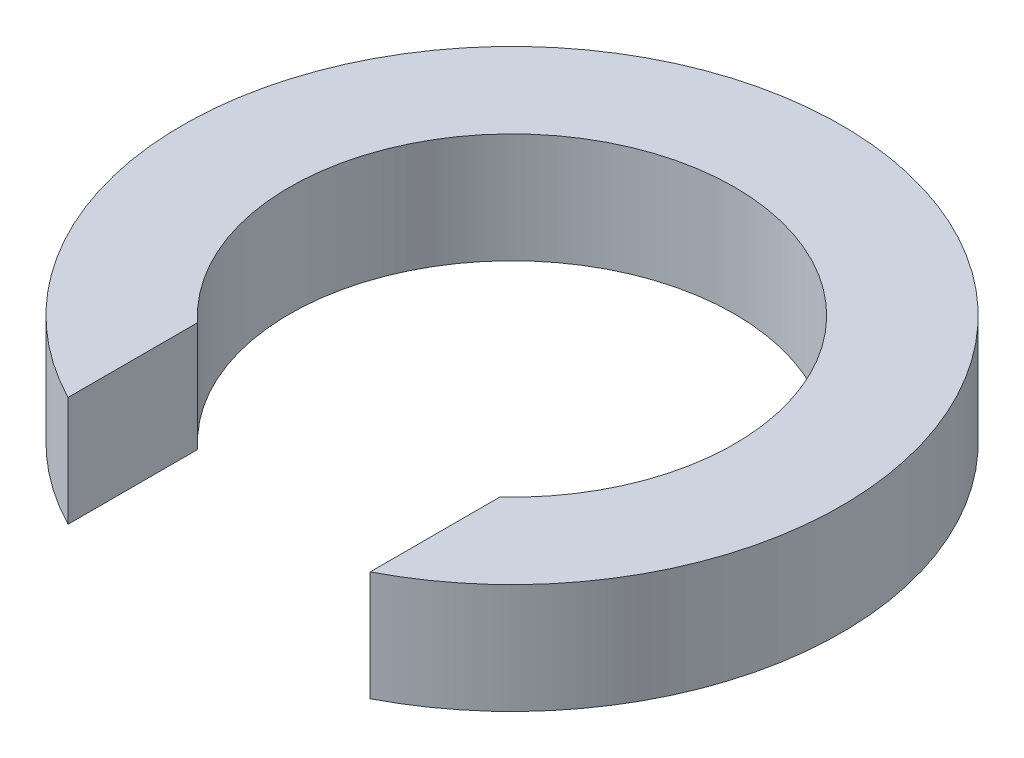
SolidWorks part; units mm, degrees
ref_plane "Front Plane" through (0, 0, 0) normal (0, 0, 1) x (1, 0, 0)
ref_plane "Top Plane" through (0, 0, 0) normal (0, 1, 0) x (1, 0, 0)
ref_plane "Right Plane" through (0, 0, 0) normal (1, 0, 0) x (0, 0, -1)
sketch "Sketch1" plane through (0, 0, 0) normal (0, 1, 0) x (1, 0, 0)
  line L0 (-2.75, -2.9732) -> (-2.75, -5.3327)
  line L1 (2.75, -2.9732) -> (2.75, -5.3327)
  arc A0 (2.75, -2.9732) -> (-2.75, -2.9732) centre (0, 0) ccw
  arc A1 (2.75, -5.3327) -> (-2.75, -5.3327) centre (0, 0) ccw
  dimension "D1" = 8.1
  dimension "D2" = 12
  dimension "D3" = 2.75
  dimension "D4" = 2.75
extrude "Boss-Extrude1" add sketch "Sketch1" along normal blind 2
